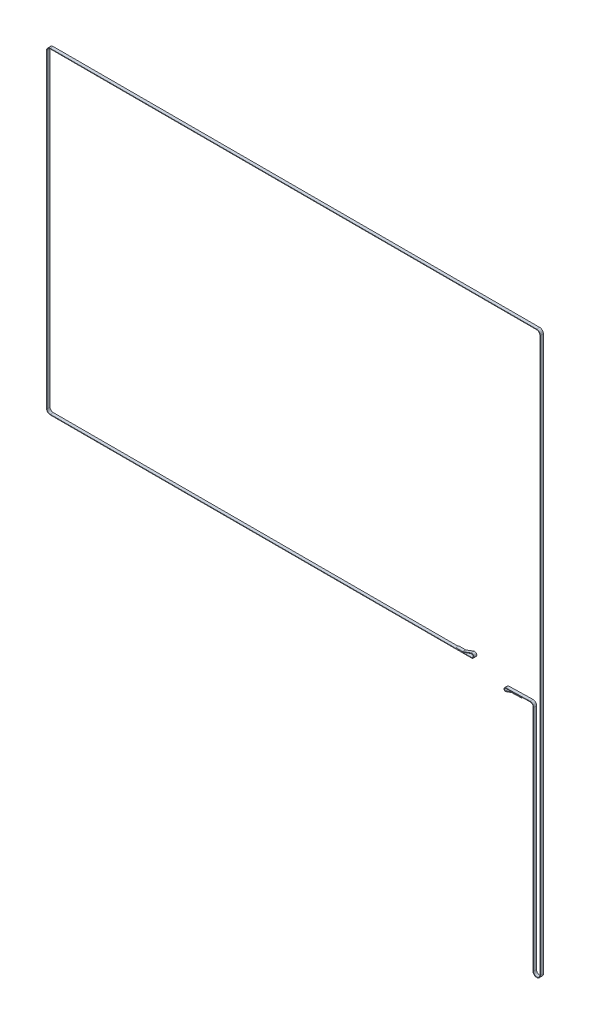
SolidWorks part; units mm, degrees
material "Rubber"
ref_plane "Front Plane" through (0, 0, 0) normal (0, 0, 1) x (1, 0, 0)
ref_plane "Top Plane" through (0, 0, 0) normal (0, 1, 0) x (1, 0, 0)
ref_plane "Right Plane" through (0, 0, 0) normal (1, 0, 0) x (0, 0, -1)
sketch "Sketch1" plane through (0, 0, 93.8685) normal (0, 0, 1) x (1, 0, 0)
  line L0 (490.9325, -538.0985) -> (490.6725, 550.8015)
  line L1 (478.1925, -538.0932) -> (478.6725, -88.9022)
  line L2 (-471.5625, 556.91) -> (484.5625, 556.91)
  line L3 (-477.6725, 550.8) -> (-477.6725, -58.8946)
  line L4 (-471.561, -65.0046) -> (356.7607, -64.8052)
  line L6 (325.6475, -64.5586) -> (338.5095, -64.5555)
  line L7 (355.6719, -58.6345) -> (351.7238, -60.0715)
  line L8 (355.6719, -58.6345) -> (340.2457, -64.2492)
  line L10 (423.3556, -82.9851) -> (471.3852, -81.7869)
  line L12 (436.1431, -85.2069) -> (454.5475, -84.7477)
  line L13 (424.523, -89.1548) -> (428.4711, -87.7178)
  line L14 (424.523, -89.1548) -> (434.5324, -85.5117)
  arc A0 (483.2985, -544.3433) -> (483.8354, -544.4284) centre (484.5625, -538.1) ccw construction
  arc A1 (478.1925, -538.0932) -> (490.9325, -538.0985) centre (484.5625, -538.1) ccw
  arc A3 (490.1071, 553.3671) -> (489.8983, 553.7768) centre (484.5625, 550.8) ccw construction
  arc A4 (476.3973, -94.1078) -> (476.7756, -93.7294) centre (471.5625, -88.8946) ccw
  arc A5 (478.6725, -88.9022) -> (471.3852, -81.7869) centre (471.5625, -88.8946) ccw
  arc A6 (490.6725, 550.8015) -> (484.5625, 556.91) centre (484.5625, 550.8) ccw
  arc A7 (-477.629, 550.0719) -> (-477.557, 549.6178) centre (-471.5625, 550.8) ccw construction
  arc A8 (-471.5625, 556.91) -> (-477.6725, 550.8) centre (-471.5625, 550.8) ccw
  arc A9 (-477.629, -59.6227) -> (-477.557, -60.0769) centre (-471.5625, -58.8946) ccw construction
  arc A10 (-477.6725, -58.8946) -> (-471.561, -65.0046) centre (-471.5625, -58.8946) ccw
  arc A12 (340.2457, -64.2492) -> (338.5095, -64.5555) centre (338.5082, -59.4755) cw
  arc A13 (356.76, -64.8052) -> (359.7459, -60.5265) centre (356.76, -61.6239) ccw
  arc A14 (356.7607, -64.8052) -> (355.6719, -58.6345) centre (356.76, -61.6239) ccw
  arc A16 (436.1431, -85.2069) -> (434.5324, -85.5117) centre (436.2698, -90.2853) ccw
  arc A18 (421.1905, -88.4199) -> (424.523, -89.1548) centre (423.435, -86.1654) ccw
  arc A19 (423.3556, -82.9851) -> (424.523, -89.1548) centre (423.435, -86.1654) ccw
  dimension "D5" = 5.08
  dimension "D9" = 31.1125
  dimension "D4" = 0.254
  dimension "D8" = 2.54
  dimension "D10" = 31.1125
  dimension "D1" = 1
  dimension "D2" = 0.8
  dimension "D3" = 0.8
  dimension "D6" = 0.8
  dimension "D7" = 0.8
extrude "Extrude-Thin4" add sketch "Sketch1" along normal blind 6 thin
